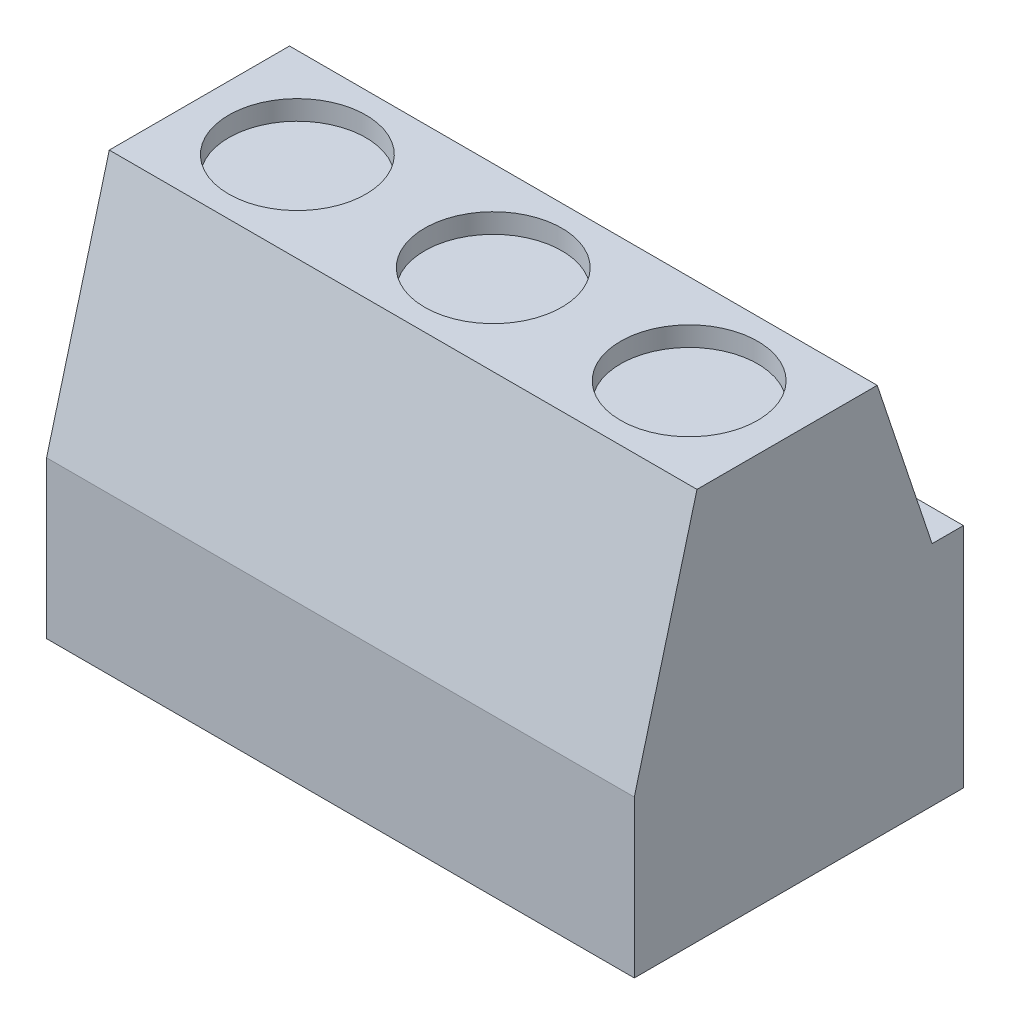
SolidWorks part; units mm, degrees
ref_plane "Front Plane" through (0, 0, 0) normal (0, 0, 1) x (1, 0, 0)
ref_plane "Top Plane" through (0, 0, 0) normal (0, 1, 0) x (1, 0, 0)
ref_plane "Right Plane" through (0, 0, 0) normal (1, 0, 0) x (0, 0, -1)
sketch "Sketch3" plane through (0, 0, 0) normal (0, 1, 0) x (1, 0, 0)
  line L0 (0, -4.2) -> (0, 4.2) construction
  line L1 (-7.5, 4.2) -> (7.5, 4.2)
  line L2 (-7.5, 4.2) -> (-7.5, -4.2)
  line L3 (-7.5, -4.2) -> (7.5, -4.2)
  line L4 (7.5, 4.2) -> (7.5, -4.2)
  line L9 (7.5, 0) -> (-7.5, 0) construction
  point P8 (0, 0)
  dimension "D1" = 8.4
  dimension "D2" = 15
extrude "Boss-Extrude3" add sketch "Sketch3" along normal blind 10 separate body
sketch "Sketch4" plane through (-7.5, 0, 0) normal (-1, 0, 0) x (0, 0, 1)
  line L0 (-3.4, 10) -> (-3.4, 5.8) construction
  line L2 (-3.4, 5.8) -> (-2, 10)
  line L3 (-2, 10) -> (-3.4, 10)
  line L6 (4.2, 10) -> (2.6, 10)
  line L7 (2.6, 10) -> (4.2, 4)
  line L10 (-2, 10) -> (2.6, 10) construction
  line L12 (4.2, 10) -> (4.2, 0) construction
  line L13 (4.2, 4) -> (4.2, 10)
  line L14 (-4.2, 10) -> (4.2, 10) construction
  line L16 (-3.4, 5.8) -> (-4.2, 5.8)
  line L17 (-4.2, 10) -> (-4.2, 0) construction
  line L18 (-4.2, 5.8) -> (-4.2, 10)
  line L19 (-4.2, 10) -> (-3.4, 10)
  line L20 (-4.2, 0) -> (4.2, 0) construction
  dimension "D1" = 5.8
  dimension "D2" = 1.6
  dimension "D3" = 1.4
  dimension "D4" = 4
  dimension "D5" = 0.8
extrude "Cut-Extrude1" cut sketch "Sketch4" against normal through all
sketch "Sketch5" plane through (0, 10, 0) normal (0, 1, 0) x (1, 0, 0)
  line L0 (-7.5, -0.3) -> (7.5, -0.3) construction
  line L1 (-7.5, 2) -> (-7.5, -2.6) construction
  line L2 (7.5, -2.6) -> (7.5, 2) construction
  circle A2 centre (-5, -0.3) radius 1.75
  dimension "D3" = 3.5
  dimension "D1" = 5
extrude "Cut-Extrude2" cut sketch "Sketch5" against normal blind 0.5
sketch "Sketch6" plane through (0, 0, -4.2) normal (0, 0, -1) x (-1, 0, 0)
  line L0 (-7.5, 0) -> (7.5, 0) construction
  line L1 (3.5, 3.4) -> (6.5, 3.4)
  line L2 (3.5, 3.4) -> (3.5, 1.4)
  line L3 (3.5, 1.4) -> (6.5, 1.4)
  line L4 (6.5, 3.4) -> (6.5, 1.4)
  point P6 (5, 1.4)
  dimension "D1" = 3
  dimension "D2" = 2
  dimension "D3" = 1.4
  dimension "D4" = 5
extrude "Cut-Extrude4" cut sketch "Sketch6" against normal blind 0.5
pattern_linear "LPattern2" count 3 spacing 5 along (1, 0, 0) of "Cut-Extrude2", "Cut-Extrude4"
